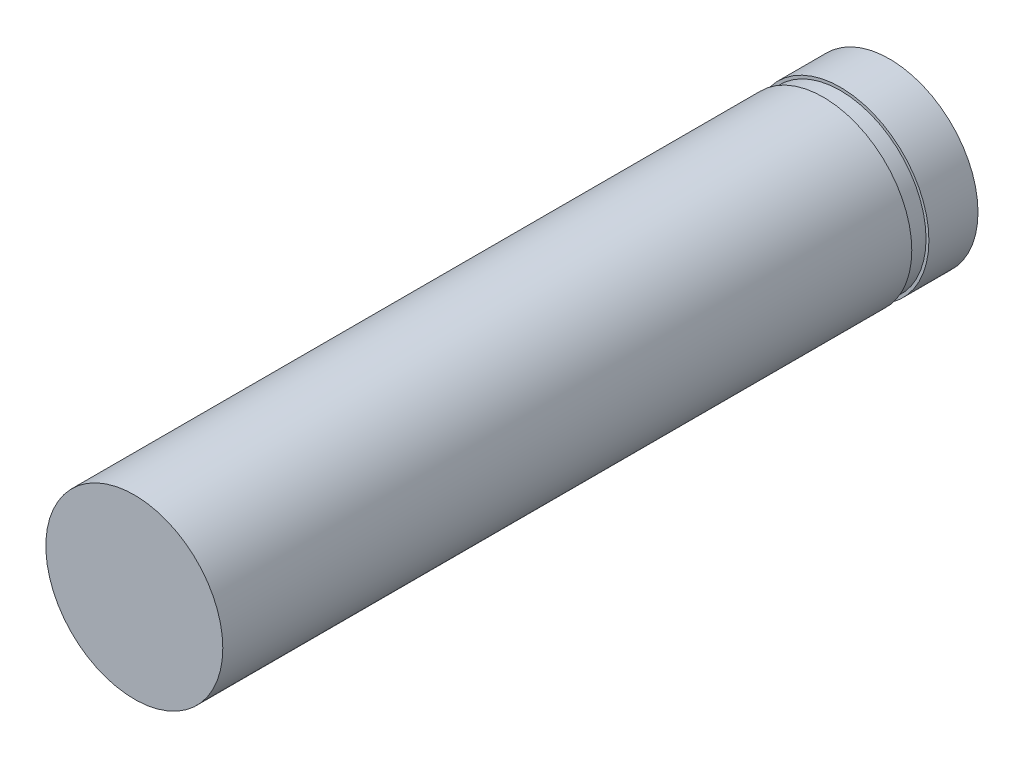
SolidWorks part; units mm, degrees
ref_plane "Plan de face" through (0, 0, 0) normal (0, 0, 1) x (1, 0, 0)
ref_plane "Plan de dessus" through (0, 0, 0) normal (0, 1, 0) x (1, 0, 0)
ref_plane "Plan de droite" through (0, 0, 0) normal (1, 0, 0) x (0, 0, -1)
sketch "Esquisse1" plane through (0, 0, 0) normal (0, 0, 1) x (1, 0, 0)
  circle A0 centre (0, 0) radius 1.55
extrude "Extrusion1" add sketch "Esquisse1" against normal blind 13.23
sketch "Esquisse2" plane through (0, 0, 0) normal (0, 1, 0) x (1, 0, 0)
  line L0 (0, -0.3131) -> (0, 13.6106) construction
  line L6 (1.5, 12.07) -> (1.55, 12.07)
  line L7 (1.55, 12.37) -> (1.55, 12.07)
  line L8 (1.5, 12.37) -> (1.5, 12.07)
  line L9 (1.5, 12.37) -> (1.55, 12.37)
revolve "Enlèvement de matière-Révolution1" cut sketch "Esquisse2" angle 360 about L0
